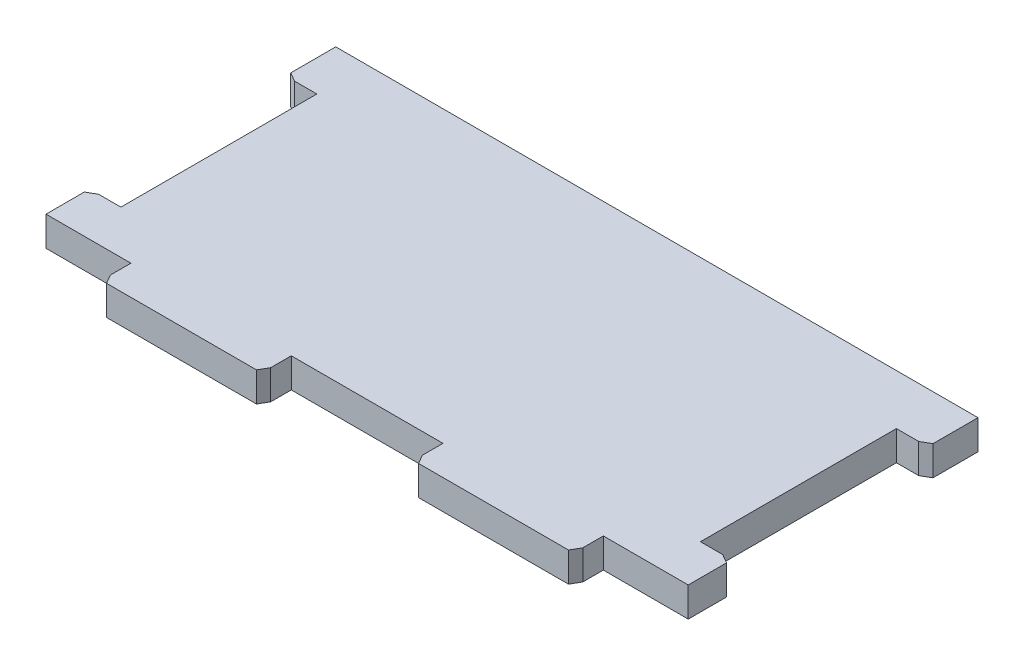
SolidWorks part; units mm, degrees
ref_plane "Front Plane" through (0, 0, 0) normal (0, 0, 1) x (1, 0, 0)
ref_plane "Top Plane" through (0, 0, 0) normal (0, 1, 0) x (1, 0, 0)
ref_plane "Right Plane" through (0, 0, 0) normal (1, 0, 0) x (0, 0, -1)
sketch "Sketch1" plane through (0, 0, 0) normal (0, 1, 0) x (1, 0, 0)
  line L1 (-46.8266, 25) -> (46.8266, 25)
  line L2 (-46.8266, 25) -> (-46.8266, -25)
  line L3 (-46.8266, -25) -> (46.8266, -25)
  line L4 (46.8266, 25) -> (46.8266, -25)
  line L5 (-46.8266, 25) -> (46.8266, -25) construction
  line L6 (-46.8266, -25) -> (46.8266, 25) construction
  point P0 (0, 0)
  dimension "D1" = 93.6531
  dimension "D2" = 50
extrude "Boss-Extrude1" add sketch "Sketch1" along normal blind 4.318
sketch "Sketch3" plane through (0, 0, 0) normal (0, -1, 0) x (1, 0, 0)
  line L0 (-46.8266, 25) -> (46.8266, 25) construction
  line L2 (-34.1266, 25) -> (-34.1266, 29.318) construction
  line L5 (-34.1266, 29.318) -> (-11.3755, 29.318) construction
  line L6 (-11.3755, 29.318) -> (-11.3755, 25) construction
  line L7 (-11.3755, 25) -> (-34.1266, 25) construction
  line L8 (-11.3755, 27.159) -> (11.3755, 27.159) construction
  line L9 (11.3755, 29.318) -> (34.1266, 29.318) construction
  line L10 (11.3755, 29.318) -> (11.3755, 25) construction
  line L11 (11.3755, 25) -> (34.1266, 25) construction
  line L12 (34.1266, 29.318) -> (34.1266, 25) construction
  line L13 (-46.8266, -25) -> (-46.8266, 25) construction
  line L14 (34.1266, 27.159) -> (46.8266, 27.159) construction
  line L15 (46.8266, 27.159) -> (46.8266, 25) construction
  line L16 (-34.1266, 27.159) -> (-46.8266, 27.159) construction
  line L17 (-46.8266, 27.159) -> (-46.8266, 25) construction
  line L18 (-34.4441, 25) -> (-34.4441, 29.318)
  line L19 (-34.4441, 29.318) -> (-11.058, 29.318)
  line L20 (-11.058, 29.318) -> (-11.058, 25)
  line L21 (11.058, 25) -> (11.058, 29.318)
  line L22 (11.058, 29.318) -> (34.4441, 29.318)
  line L23 (34.4441, 29.318) -> (34.4441, 25)
  line L24 (-22.751, 29.318) -> (-22.751, 25) construction
  line L25 (22.751, 29.318) -> (22.751, 25) construction
  line L26 (-11.058, 25) -> (-34.4441, 25)
  line L27 (11.058, 25) -> (34.4441, 25)
  dimension "D1" = 4.318
  dimension "D2" = 12.7
  dimension "D3" = 0.3175
extrude "Boss-Extrude2" add sketch "Sketch3" against normal up to surface (4.318 mm away) up to face at (0, 4.318, 0)
sketch "Sketch4" plane through (0, 4.318, 0) normal (0, 1, 0) x (1, 0, 0)
  line L14 (-46.8266, -18.65) -> (46.8266, -18.65) construction
  line L15 (46.8266, -25) -> (46.8266, 25) construction
  line L16 (-46.8266, 9.925) -> (46.8266, 9.925) construction
  line L19 (46.8266, 25) -> (-46.8266, 25) construction
  line L20 (-46.8266, 21.825) -> (46.8266, 21.825) construction
  line L21 (-46.8266, 21.825) -> (-46.8266, 17.253) construction
  line L22 (-46.8266, 17.253) -> (46.8266, 17.253) construction
  line L23 (46.8266, 21.825) -> (46.8266, 17.253) construction
  line L24 (-46.8266, -25) -> (-34.4441, -25) construction
  line L25 (-46.8266, 25) -> (-46.8266, -25) construction
  line L37 (-46.8266, -18.65) -> (-42.2546, -18.65)
  line L38 (-46.8266, -18.65) -> (-46.8266, 9.925)
  line L39 (-46.8266, 9.925) -> (-42.2546, 9.925)
  line L40 (-42.2546, -18.65) -> (-42.2546, 9.925)
  line L41 (46.8266, 9.925) -> (42.2546, 9.925)
  line L42 (46.8266, 9.925) -> (46.8266, -18.65)
  line L43 (46.8266, -18.65) -> (42.2546, -18.65)
  line L44 (42.2546, 9.925) -> (42.2546, -18.65)
  dimension "D1" = 28.575
  dimension "D2" = 6.35
  dimension "D4" = 4.572
  dimension "D6" = 3.175
extrude "Cut-Extrude1" cut sketch "Sketch4" against normal up to next
sketch "Sketch5" plane through (0, 4.318, 0) normal (0, 1, 0) x (1, 0, 0)
  line L1 (-46.8266, 25) -> (46.8266, 25)
  line L2 (-46.8266, 25) -> (-46.8266, 17.253)
  line L3 (-46.8266, 17.253) -> (46.8266, 17.253)
  line L4 (46.8266, 25) -> (46.8266, 17.253)
  line L7 (46.8266, 9.925) -> (46.8266, 25) construction
  line L8 (-46.8266, 25) -> (-46.8266, 9.925) construction
  line L9 (-46.8266, 17.253) -> (46.8266, 17.253) construction
  line L10 (46.8266, 25) -> (-46.8266, 25) construction
extrude "Cut-Extrude2" cut sketch "Sketch5" against normal up to next
sketch "Sketch8" plane through (0, 0, 0) normal (0, -1, 0) x (1, 0, 0)
  line L9 (-39.7146, 4.3625) -> (-42.2546, 4.3625) construction
  line L10 (-42.2546, -9.925) -> (-42.2546, 18.65) construction
  line L20 (39.7146, 4.3625) -> (42.2546, 4.3625) construction
  line L21 (42.2546, 18.65) -> (42.2546, -9.925) construction
  line L22 (-22.751, 26.778) -> (-22.751, 29.318) construction
  line L35 (-11.058, 29.318) -> (-34.4441, 29.318) construction
  line L37 (22.751, 26.778) -> (22.751, 29.318) construction
  line L38 (34.4441, 29.318) -> (11.058, 29.318) construction
  line L39 (-39.7146, 3.3465) -> (-39.7146, 5.3785) construction
  line L40 (-23.767, 26.778) -> (-21.735, 26.778) construction
  line L41 (21.735, 26.778) -> (23.767, 26.778) construction
  line L42 (39.7146, 6.3945) -> (39.7146, 4.3625) construction
  line L43 (39.7146, 4.3625) -> (39.7146, 2.3305) construction
  circle A0 centre (21.735, 26.778) radius 0.635
  circle A1 centre (23.767, 26.778) radius 0.635
  circle A2 centre (39.7146, 6.3945) radius 0.635
  circle A3 centre (39.7146, 4.3625) radius 0.635
  circle A4 centre (39.7146, 2.3305) radius 0.635
  circle A5 centre (-23.767, 26.778) radius 0.635
  circle A6 centre (-21.735, 26.778) radius 0.635
  circle A7 centre (-39.7146, 5.3785) radius 0.635
  circle A8 centre (-39.7146, 3.3465) radius 0.635
  dimension "D5" = 1.27
  dimension "D1" = 2.54
  dimension "D6" = 2.032
extrude "Cut-Extrude4" cut sketch "Sketch8" against normal blind 0.127
chamfer "Chamfer1" distance 0.762 angle 60 4 edges at (-34.4441, 2.159, 29.318) (11.058, 2.159, 29.318) (46.8266, 2.159, 18.65) (-46.8266, 2.159, -9.925)
chamfer "Chamfer2" distance 0.762 angle 60 4 edges at (34.4441, 2.159, 29.318) (-11.058, 2.159, 29.318) (-46.8266, 2.159, 18.65) (46.8266, 2.159, -9.925)
